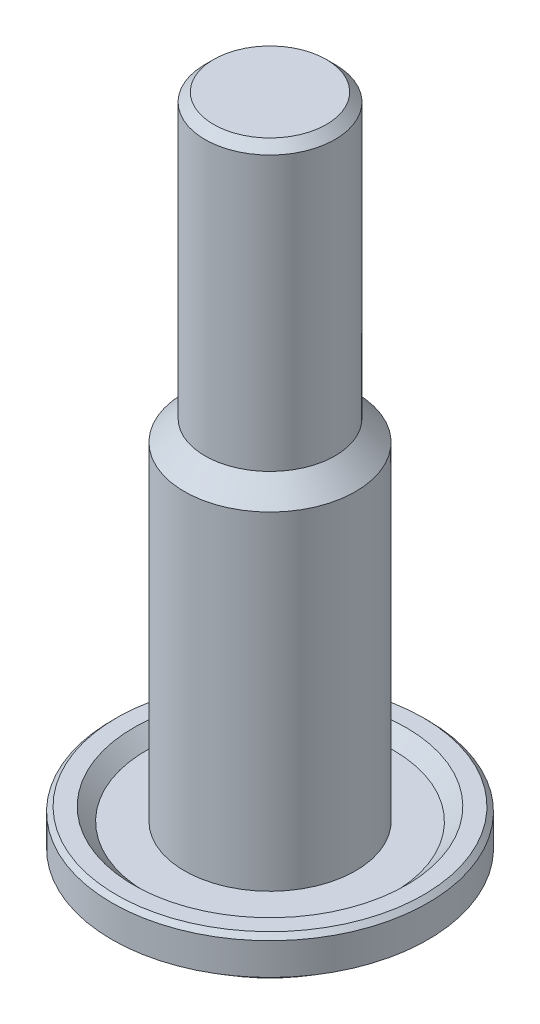
SolidWorks part; units mm, degrees
ref_plane "Front Plane" through (0, 0, 0) normal (0, 0, 1) x (1, 0, 0)
ref_plane "Top Plane" through (0, 0, 0) normal (0, 1, 0) x (1, 0, 0)
ref_plane "Right Plane" through (0, 0, 0) normal (1, 0, 0) x (0, 0, -1)
sketch "Sketch2" plane through (0, 0, 0) normal (1, 0, 0) x (0, 0, -1)
  line L0 (0, 40.0558) -> (-3.302, 40.0558)
  line L1 (-3.302, 40.0558) -> (-3.81, 39.5478)
  line L2 (-3.81, 39.5478) -> (-3.81, 23.495)
  line L3 (-3.81, 23.495) -> (-5.0165, 22.2885)
  line L4 (-5.0165, 22.2885) -> (-5.0165, 3.048)
  line L5 (-5.0165, 3.048) -> (-7.2263, 3.048)
  line L6 (-7.2263, 3.048) -> (-7.9883, 3.81)
  line L7 (-7.9883, 3.81) -> (-8.9889, 3.81)
  line L8 (-8.9889, 3.81) -> (-9.2583, 3.5406)
  line L9 (-9.2583, 3.5406) -> (-9.2583, 1.6764)
  line L10 (-9.2583, 1.6764) -> (-6.9342, 0)
  line L11 (-6.9342, 0) -> (-2.54, 0)
  line L12 (-2.54, 0) -> (-2.54, 20.955)
  line L13 (-2.54, 20.955) -> (0, 20.955)
  line L14 (0, 20.955) -> (0, 40.0558)
  point P2 (0, 30.5054)
  point P17 (-3.7867, 39.3666)
  point P18 (0, 0)
  dimension "D1" = 3.81
  dimension "D2" = 40.0558
  dimension "D3" = 135
  dimension "D4" = 23.495
  dimension "D5" = 3.81
  dimension "D6" = 9.2583
  dimension "D7" = 6.9342
  dimension "D8" = 1.6764
  dimension "D9" = 0.381
  dimension "D10" = 1.27
  dimension "D11" = 0.762
  dimension "D12" = 5.0165
  dimension "D13" = 20.955
  dimension "D14" = 2.54
  dimension "D15" = 0.508
revolve "Revolve1" add sketch "Sketch2" angle 360 about L14
